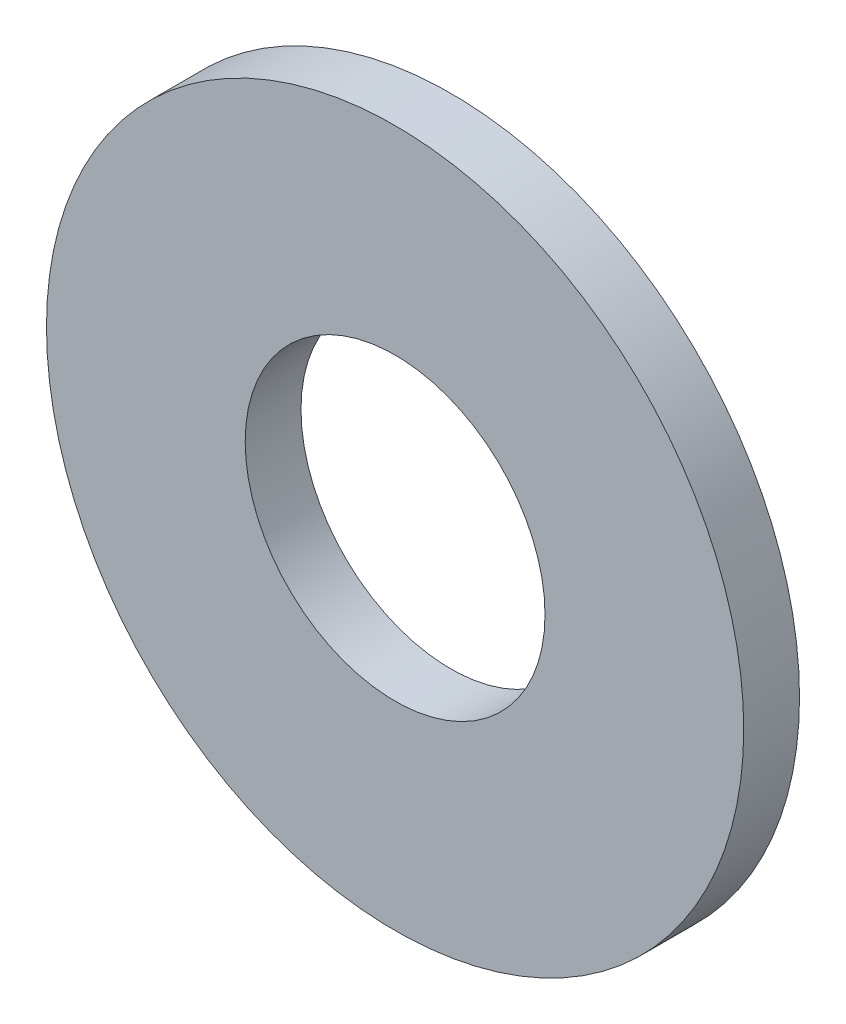
SolidWorks part; units mm, degrees
material "Laiton"
ref_plane "Plan de face" through (0, 0, 0) normal (0, 0, 1) x (1, 0, 0)
ref_plane "Plan de dessus" through (0, 0, 0) normal (0, 1, 0) x (1, 0, 0)
ref_plane "Plan de droite" through (0, 0, 0) normal (1, 0, 0) x (0, 0, -1)
sketch "Esquisse1" plane through (0, 0, 0) normal (0, 0, 1) x (1, 0, 0)
  circle A0 centre (0, 0) radius 2.15
  circle A1 centre (0, 0) radius 5
  dimension "D1" = 10
  dimension "D2" = 4.3
extrude "Extrusion1" add sketch "Esquisse1" along normal blind 0.8
